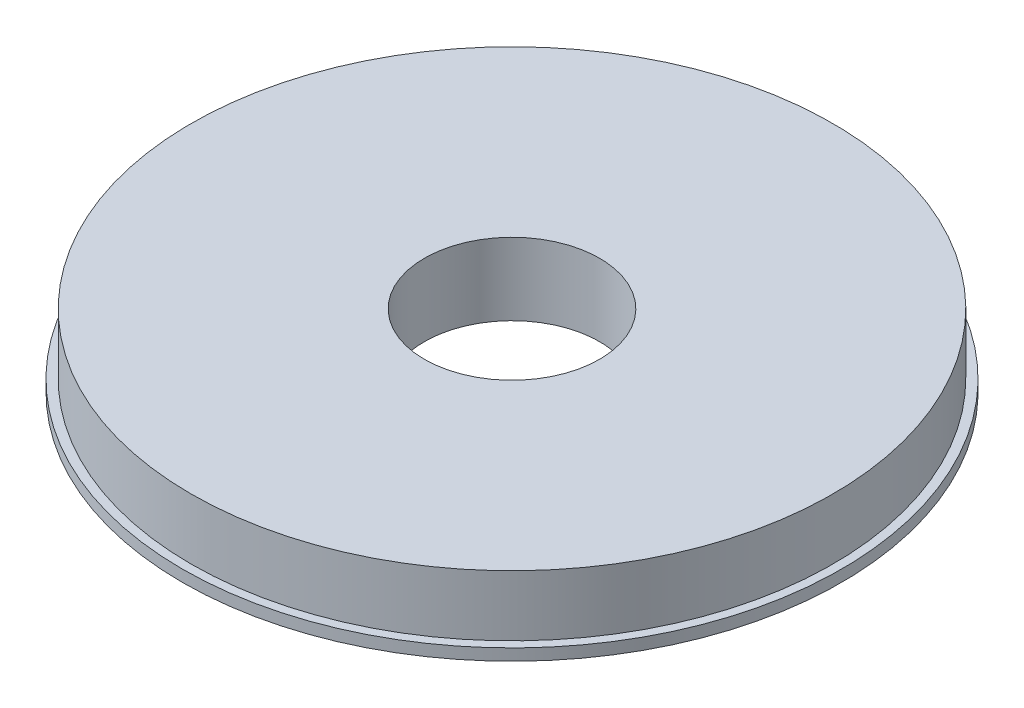
SolidWorks part; units mm, degrees
ref_plane "Front Plane" through (0, 0, 0) normal (0, 0, 1) x (1, 0, 0)
ref_plane "Top Plane" through (0, 0, 0) normal (0, 1, 0) x (1, 0, 0)
ref_plane "Right Plane" through (0, 0, 0) normal (1, 0, 0) x (0, 0, -1)
sketch "Sketch1" plane through (0, 0, 0) normal (0, 1, 0) x (1, 0, 0)
  circle A0 centre (0, 0) radius 55.5
  circle A1 centre (0, 0) radius 15.15
  dimension "D1" = 111
  dimension "D2" = 30.3
extrude "Boss-Extrude1" add sketch "Sketch1" along normal blind 12.5
sketch "Sketch3" plane through (0, 12.5, 0) normal (0, 1, 0) x (1, 0, 0)
  circle A0 centre (0, 0) radius 57
  circle A1 centre (0, 0) radius 55.5
  circle A2 centre (0, 0) radius 55.5 construction
  dimension "D1" = 114
extrude "Boss-Extrude3" add sketch "Sketch3" along normal blind 2 from offset 12.5
